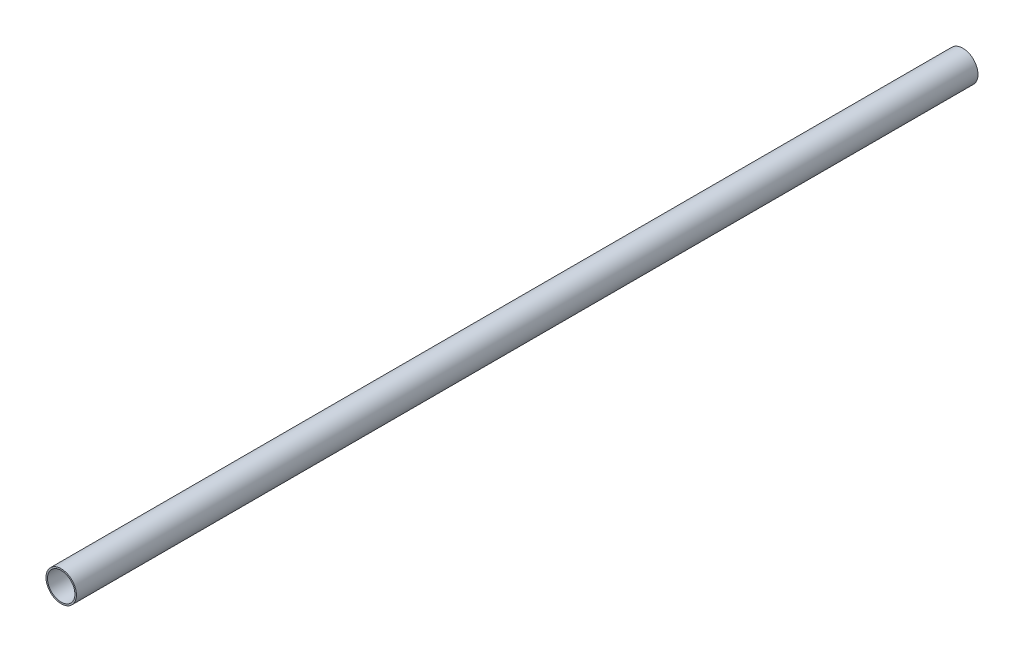
SolidWorks part; units mm, degrees
ref_plane "Front Plane" through (0, 0, 0) normal (0, 0, 1) x (1, 0, 0)
ref_plane "Top Plane" through (0, 0, 0) normal (0, 1, 0) x (1, 0, 0)
ref_plane "Right Plane" through (0, 0, 0) normal (1, 0, 0) x (0, 0, -1)
sketch "Sketch1" plane through (0, 0, 0) normal (0, 0, 1) x (1, 0, 0)
  circle A0 centre (0, 0) radius 12.7
  circle A1 centre (0, 0) radius 11.4554
  dimension "D1" = 25.4
  dimension "D2" = 22.9108
extrude "Boss-Extrude1" add sketch "Sketch1" along normal blind 752.856
